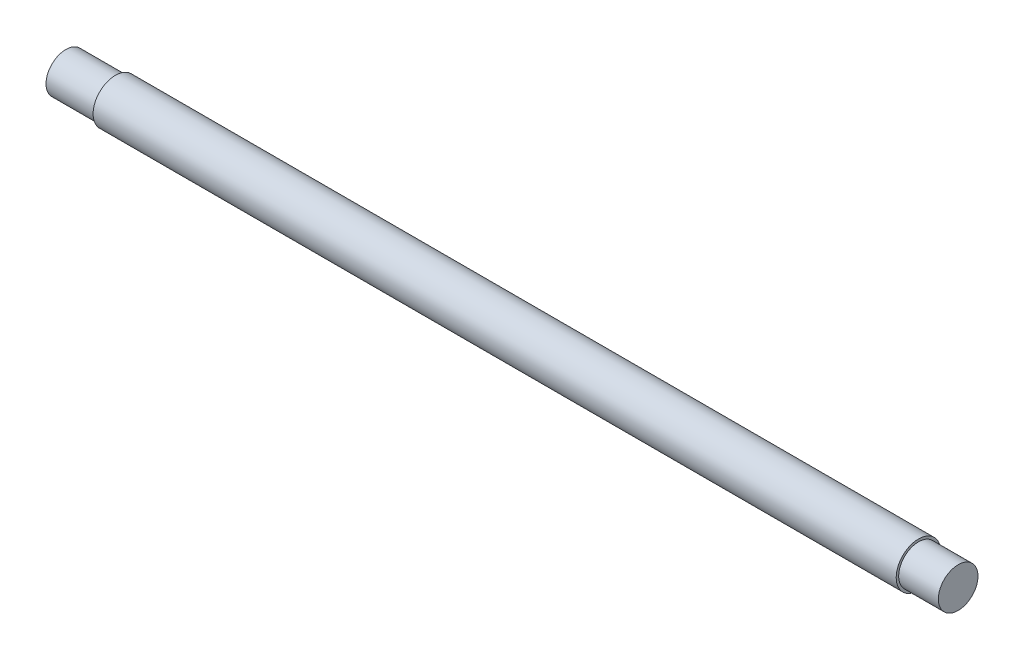
SolidWorks part; units mm, degrees
ref_plane "Front Plane" through (0, 0, 0) normal (0, 0, 1) x (1, 0, 0)
ref_plane "Top Plane" through (0, 0, 0) normal (0, 1, 0) x (1, 0, 0)
ref_plane "Right Plane" through (0, 0, 0) normal (1, 0, 0) x (0, 0, -1)
sketch "Sketch1" plane through (0, 0, 0) normal (1, 0, 0) x (0, 0, -1)
  circle A0 centre (0, 0) radius 2.25
  dimension "D1" = 4.5
extrude "Boss-Extrude1" add sketch "Sketch1" along normal mid plane 90
sketch "Sketch2" plane through (45, 0, 0) normal (1, 0, 0) x (0, 0, -1)
  circle A0 centre (0, 0) radius 2
  circle A1 centre (0, 0) radius 2.25
  dimension "D1" = 4
extrude "Cut-Extrude1" cut sketch "Sketch2" against normal blind 4
sketch "Sketch3" plane through (-45, 0, 0) normal (-1, 0, 0) x (0, 0, 1)
  circle A0 centre (0, 0) radius 2
  circle A1 centre (0, 0) radius 2.25
  dimension "D1" = 4
extrude "Cut-Extrude2" cut sketch "Sketch3" against normal blind 5
